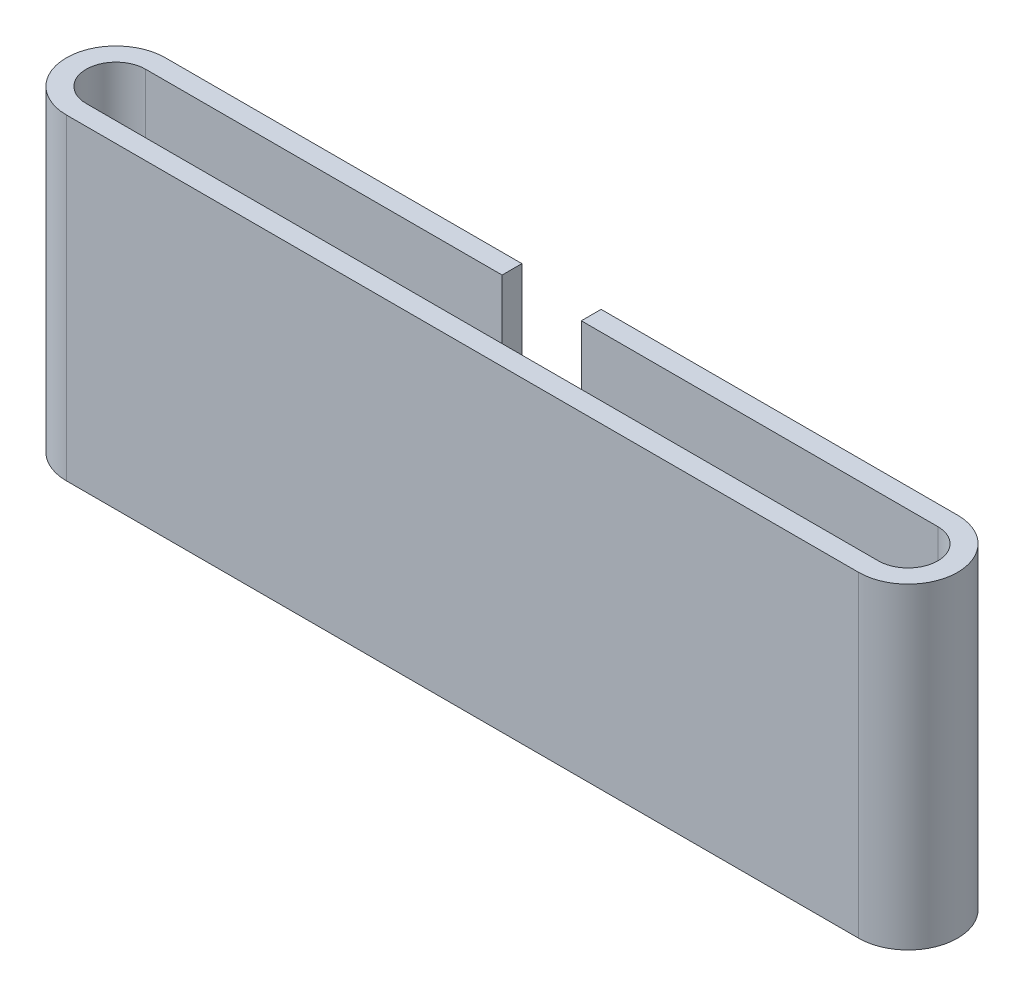
SolidWorks part; units mm, degrees
ref_plane "前基準面" through (0, 0, 0) normal (0, 0, 1) x (1, 0, 0)
ref_plane "上基準面" through (0, 0, 0) normal (0, 1, 0) x (1, 0, 0)
ref_plane "右基準面" through (0, 0, 0) normal (1, 0, 0) x (0, 0, -1)
sketch "草圖1" plane through (0, 0, 0) normal (0, 1, 0) x (1, 0, 0)
  line L0 (-20, 0) -> (60, 0) construction
  line L1 (-55, 0) -> (55, 0) construction
  line L2 (-20, 5) -> (60, 5)
  line L3 (-20, -5) -> (60, -5)
  line L4 (-20, 0) -> (60, 0) construction
  line L5 (-20, 3) -> (60, 3)
  line L6 (-20, -3) -> (60, -3)
  arc A0 (-20, 5) -> (-20, -5) centre (-20, 0) ccw
  arc A1 (60, -5) -> (60, 5) centre (60, 0) ccw
  arc A2 (-20, 3) -> (-20, -3) centre (-20, 0) ccw
  arc A3 (60, -3) -> (60, 3) centre (60, 0) ccw
  point P5 (20, 0)
  point P12 (20, 0)
  dimension "D1" = 80
extrude "填料-伸長1" add sketch "草圖1" along normal blind 30
sketch "草圖2" plane through (0, 0, 0) normal (0, -1, 0) x (1, 0, 0)
  line L2 (-20, -5) -> (60, -5)
  line L3 (60, 5) -> (-20, 5)
  line L4 (-20, -5) -> (60, -5)
  line L5 (60, 5) -> (-20, 5)
  arc A2 (-20, 5) -> (-20, -5) centre (-20, 0) ccw
  arc A3 (60, -5) -> (60, 5) centre (60, 0) ccw
  arc A4 (-20, 5) -> (-20, -5) centre (-20, 0) ccw
  arc A5 (60, -5) -> (60, 5) centre (60, 0) ccw
  dimension "D1" = 0
extrude "填料-伸長2" add sketch "草圖2" along normal blind 2
sketch "草圖3" plane through (0, 30, 0) normal (0, 1, 0) x (1, 0, 0)
  line L0 (60, 5) -> (-20, 5) construction
  line L1 (16, 2.6476) -> (24, 2.6476)
  line L2 (16, 2.6476) -> (16, 5)
  line L3 (16, 5) -> (24, 5)
  line L4 (24, 2.6476) -> (24, 5)
  line L5 (16, 2.6476) -> (24, 5) construction
  line L6 (16, 5) -> (24, 2.6476) construction
  line L7 (0, -5.5) -> (0, 5.5) construction
  point P0 (20, 3.8238)
  dimension "D1" = 20
  dimension "D2" = 8
extrude "除料-伸長1" cut sketch "草圖3" against normal blind 30
